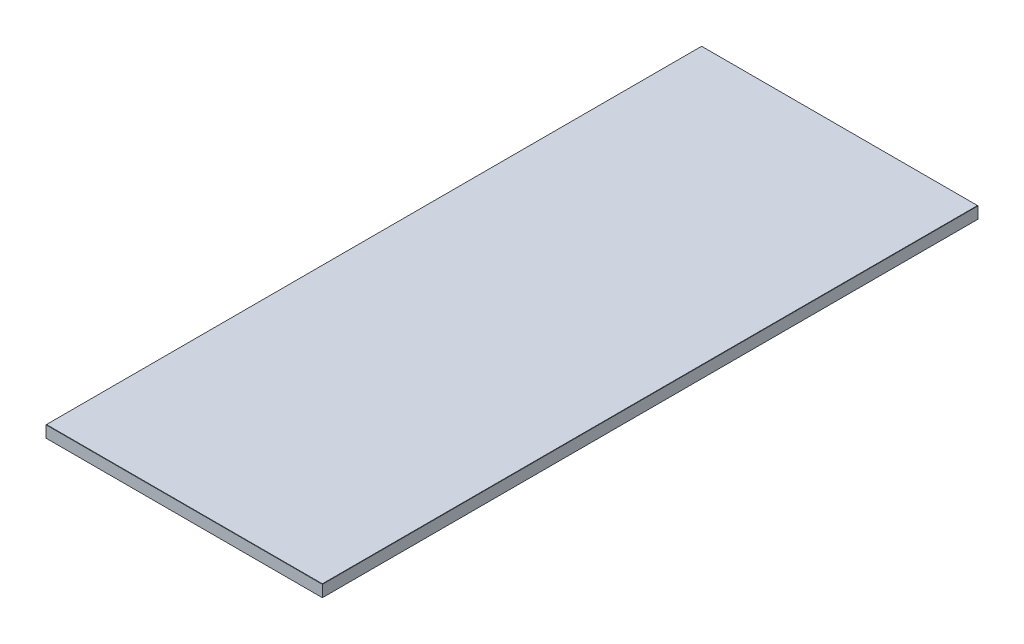
SolidWorks part; units mm, degrees
ref_plane "Front Plane" through (0, 0, 0) normal (0, 0, 1) x (1, 0, 0)
ref_plane "Top Plane" through (0, 0, 0) normal (0, 1, 0) x (1, 0, 0)
ref_plane "Right Plane" through (0, 0, 0) normal (1, 0, 0) x (0, 0, -1)
sketch "Sketch1" plane through (0, 0, 0) normal (0, 1, 0) x (1, 0, 0)
  line L1 (-137, -325) -> (137, -325)
  line L2 (-137, -325) -> (-137, 325)
  line L3 (-137, 325) -> (137, 325)
  line L4 (137, -325) -> (137, 325)
  line L5 (-137, -325) -> (137, 325) construction
  line L6 (-137, 325) -> (137, -325) construction
  point P0 (0, 0)
  dimension "D1" = 274
  dimension "D2" = 650
extrude "Boss-Extrude1" add sketch "Sketch1" along normal blind 12
chamfer "Chamfer1" distance 0.25 angle 45 8 edges at (0, 0, -325) (-137, 0, 0) (0, 0, 325) (137, 0, 0) (0, 12, 325) (-137, 12, 0) (0, 12, -325) (137, 12, 0)
